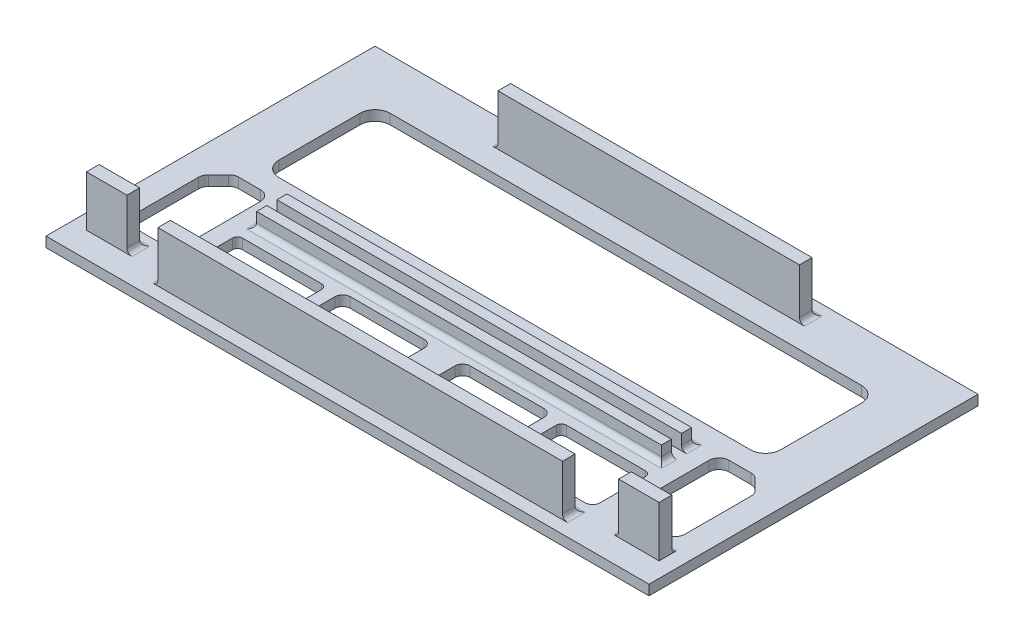
SolidWorks part; units mm, degrees
ref_plane "Front Plane" through (0, 0, 0) normal (0, 0, 1) x (1, 0, 0)
ref_plane "Top Plane" through (0, 0, 0) normal (0, 1, 0) x (1, 0, 0)
ref_plane "Right Plane" through (0, 0, 0) normal (1, 0, 0) x (0, 0, -1)
sketch "Sketch1" plane through (0, 0, 0) normal (0, 1, 0) x (1, 0, 0)
  line L1 (-59.6, -32.52) -> (59.6, -32.52)
  line L2 (-59.6, -32.52) -> (-59.6, 32.52)
  line L3 (-59.6, 32.52) -> (59.6, 32.52)
  line L4 (59.6, -32.52) -> (59.6, 32.52)
  line L5 (-59.6, -32.52) -> (59.6, 32.52) construction
  line L6 (-59.6, 32.52) -> (59.6, -32.52) construction
  point P0 (0, 0)
  dimension "D1" = 119.2
  dimension "D2" = 65.04
extrude "Boss-Extrude1" add sketch "Sketch1" along normal blind 2
ref_plane "Plane1" through (0, 0, 0) normal (-1, 0, 0) x (0, 0, 1)
sketch "Sketch2" plane through (0, 2, 0) normal (0, 1, 0) x (1, 0, 0)
  line L0 (-29.8, 29.52) -> (29.8, 29.52)
  line L1 (59.6, 32.52) -> (-59.6, 32.52) construction
  line L2 (59.6, -32.52) -> (59.6, 32.52) construction
  line L3 (59.6, -27.02) -> (59.6, -29.52)
  line L4 (29.8, 27.02) -> (-29.8, 27.02)
  line L5 (40, -4.48) -> (-40, -4.48)
  line L6 (40, -8.48) -> (40, -10.48)
  line L7 (-29.8, 29.52) -> (-29.8, 27.02)
  line L8 (29.8, 29.52) -> (29.8, 27.02)
  line L9 (-40, -4.48) -> (-40, -6.48)
  line L10 (-40, -6.48) -> (40, -6.48)
  line L11 (40, -6.48) -> (40, -4.48)
  line L12 (40, -10.48) -> (-40, -10.48)
  line L13 (-40, -10.48) -> (-40, -8.48)
  line L14 (-40, -8.48) -> (40, -8.48)
  line L15 (0, 1.1) -> (0, -1.1) construction
  point P16 (0, -10.48)
  dimension "D1" = 3
  dimension "D2" = 2.5
  dimension "D3" = 39
  dimension "D4" = 29.8
  dimension "D5" = 2
  dimension "D6" = 2
  dimension "D7" = 2
  dimension "D8" = 80
  dimension "D9" = 80
extrude "Boss-Extrude2" add sketch "Sketch2" along normal blind 10 contours L14 L13 L12 L6 | L10 L11 L5 L9 | L8 L0 L7 L4
fillet "Fillet1" radius 1 9 edges at (-29.8, 2, -28.27) (29.8, 2, -28.27) (0, 2, -29.52) (-40, 2, 5.48) (-40, 2, 9.48) (40, 2, 9.48) (40, 2, 5.48) (0, 2, 4.48) (0, 2, 10.48)
sketch "Sketch3" plane through (0, 12, 0) normal (0, 1, 0) x (1, 0, 0)
  line L0 (-40, -6.48) -> (40, -6.48) construction
  line L1 (40, -6.48) -> (40, -4.48) construction
  line L2 (40, -4.48) -> (-40, -4.48) construction
  line L3 (-40, -4.48) -> (-40, -6.48) construction
  line L4 (40, -8.48) -> (-40, -8.48) construction
  line L5 (-40, -8.48) -> (-40, -10.48) construction
  line L6 (-40, -10.48) -> (40, -10.48) construction
  line L7 (40, -10.48) -> (40, -8.48) construction
  line L8 (-40, -6.48) -> (40, -6.48)
  line L9 (40, -6.48) -> (40, -4.48)
  line L10 (40, -4.48) -> (-40, -4.48)
  line L11 (-40, -4.48) -> (-40, -6.48)
  line L12 (40, -8.48) -> (-40, -8.48)
  line L13 (-40, -8.48) -> (-40, -10.48)
  line L14 (-40, -10.48) -> (40, -10.48)
  line L15 (40, -10.48) -> (40, -8.48)
extrude "Cut-Extrude1" cut sketch "Sketch3" against normal blind 7
sketch "Sketch4" plane through (0, 2, 0) normal (0, 1, 0) x (1, 0, 0)
  line L0 (40, -30.02) -> (-40, -30.02)
  line L1 (-40, -30.02) -> (-40, -27.52)
  line L2 (-40, -27.52) -> (40, -27.52)
  line L3 (40, -27.52) -> (40, -30.02)
  line L4 (-59.6, -32.52) -> (59.6, -32.52) construction
  line L5 (0, 1.1) -> (0, -1.1) construction
  line L6 (48.6, -27.52) -> (56.6, -27.52)
  line L7 (56.6, -27.52) -> (56.6, -25.02)
  line L8 (56.6, -25.02) -> (48.6, -25.02)
  line L9 (48.6, -25.02) -> (48.6, -27.52)
  line L15 (59.6, -32.52) -> (59.6, 32.52) construction
  point P6 (0, -27.52)
  point P15 (52.6, -27.52)
  dimension "D1" = 2.5
  dimension "D2" = 2.5
  dimension "D3" = 80
  dimension "D4" = 2.5
  dimension "D6" = 3
  dimension "D7" = 8
extrude "Boss-Extrude3" add sketch "Sketch4" along normal blind 10
fillet "Fillet2" radius 1 5 edges at (-40, 2, 28.77) (48.6, 2, 26.27) (52.6, 2, 25.02) (40, 2, 28.77) (0, 2, 27.52)
mirror "Mirror1" about plane through (0, 0, 0) normal (-1, 0, 0) of "Boss-Extrude3"
fillet "Fillet3" radius 1 2 edges at (-52.6, 2, 25.02) (-48.6, 2, 26.27)
sketch "Sketch5" plane through (0, 2, 0) normal (0, 1, 0) x (1, 0, 0)
  line L0 (46.6, 22.52) -> (6.3115, 22.52)
  line L1 (6.3115, 22.52) -> (-46.6, 22.52)
  line L2 (-49.6, 19.52) -> (-49.6, 3.52)
  line L3 (-46.6, 0.52) -> (46.6, 0.52)
  line L4 (49.6, 3.52) -> (49.6, 19.52)
  line L5 (59.6, 32.52) -> (-59.6, 32.52) construction
  line L6 (59.6, -32.52) -> (59.6, 32.52) construction
  line L7 (-59.6, 32.52) -> (-59.6, -32.52) construction
  arc A0 (-49.6, 3.52) -> (-46.6, 0.52) centre (-46.6, 3.52) ccw
  arc A1 (-46.6, 22.52) -> (-49.6, 19.52) centre (-46.6, 19.52) ccw
  arc A2 (46.6, 22.52) -> (49.6, 19.52) centre (46.6, 19.52) cw
  arc A3 (46.6, 0.52) -> (49.6, 3.52) centre (46.6, 3.52) ccw
  dimension "D5" = 3
  dimension "D1" = 10
  dimension "D2" = 10
  dimension "D3" = 10
  dimension "D4" = 22
extrude "Cut-Extrude2" cut sketch "Sketch5" against normal blind 10
sketch "Sketch6" plane through (0, 2, 0) normal (0, 1, 0) x (1, 0, 0)
  line L3 (54.0142, -5.9408) -> (52.0453, -3.9719)
  line L4 (50.6311, -3.3862) -> (46.3278, -3.3862)
  line L5 (54.6, -7.3551) -> (54.6, -20.3979)
  line L6 (52.6, -22.3979) -> (46.3278, -22.3979)
  line L7 (44.3278, -20.3979) -> (44.3278, -5.3862)
  line L10 (39.8278, -13.4493) -> (24.2108, -13.4493)
  line L16 (4.044, -24.8936) -> (19.6609, -24.8936)
  line L17 (40.8278, -14.4493) -> (40.8278, -23.3936)
  line L18 (39.3278, -24.8936) -> (24.7108, -24.8936)
  line L19 (23.2108, -23.3936) -> (23.2108, -14.4493)
  line L21 (20.6609, -23.8936) -> (20.6609, -14.3214)
  line L22 (19.1609, -12.8214) -> (4.544, -12.8214)
  line L23 (3.044, -14.3214) -> (3.044, -23.8936)
  line L25 (59.6, -32.52) -> (59.6, 32.52) construction
  line L26 (0, -47.4967) -> (0, 52.968) construction
  line L29 (-4.044, -24.8936) -> (-19.6609, -24.8936)
  line L31 (-3.044, -14.3214) -> (-3.044, -23.8936)
  line L33 (-19.1609, -12.8214) -> (-4.544, -12.8214)
  line L34 (-20.6609, -23.8936) -> (-20.6609, -14.3214)
  line L37 (-39.3278, -24.8936) -> (-24.7108, -24.8936)
  line L39 (-39.8278, -13.4493) -> (-24.2108, -13.4493)
  line L40 (-23.2108, -14.4493) -> (-23.2108, -23.3936)
  line L42 (-40.8278, -23.3936) -> (-40.8278, -14.4493)
  line L43 (-44.3278, -5.3862) -> (-44.3278, -20.3979)
  line L44 (-50.6311, -3.3862) -> (-46.3278, -3.3862)
  line L45 (-54.0142, -5.9408) -> (-52.0453, -3.9719)
  line L46 (-54.6, -20.3979) -> (-54.6, -7.3551)
  line L51 (-52.6, -22.3979) -> (-46.3278, -22.3979)
  arc A1 (44.3278, -5.3862) -> (46.3278, -3.3862) centre (46.3278, -5.3862) cw
  arc A2 (52.0453, -3.9719) -> (50.6311, -3.3862) centre (50.6311, -5.3862) ccw
  arc A3 (54.6, -7.3551) -> (54.0142, -5.9408) centre (52.6, -7.3551) ccw
  arc A5 (46.3278, -22.3979) -> (44.3278, -20.3979) centre (46.3278, -20.3979) cw
  arc A8 (54.6, -20.3979) -> (52.6, -22.3979) centre (52.6, -20.3979) cw
  arc A10 (4.544, -12.8214) -> (3.044, -14.3214) centre (4.544, -14.3214) ccw
  arc A11 (20.6609, -14.3214) -> (19.1609, -12.8214) centre (19.1609, -14.3214) ccw
  arc A15 (24.7108, -24.8936) -> (23.2108, -23.3936) centre (24.7108, -23.3936) cw
  arc A16 (40.8278, -23.3936) -> (39.3278, -24.8936) centre (39.3278, -23.3936) cw
  arc A18 (3.044, -23.8936) -> (4.044, -24.8936) centre (4.044, -23.8936) ccw
  arc A19 (20.6609, -23.8936) -> (19.6609, -24.8936) centre (19.6609, -23.8936) cw
  arc A21 (40.8278, -14.4493) -> (39.8278, -13.4493) centre (39.8278, -14.4493) ccw
  arc A23 (24.2108, -13.4493) -> (23.2108, -14.4493) centre (24.2108, -14.4493) ccw
  arc A26 (-3.044, -23.8936) -> (-4.044, -24.8936) centre (-4.044, -23.8936) cw
  arc A27 (-20.6609, -23.8936) -> (-19.6609, -24.8936) centre (-19.6609, -23.8936) ccw
  arc A29 (-4.544, -12.8214) -> (-3.044, -14.3214) centre (-4.544, -14.3214) cw
  arc A31 (-20.6609, -14.3214) -> (-19.1609, -12.8214) centre (-19.1609, -14.3214) cw
  arc A35 (-40.8278, -23.3936) -> (-39.3278, -24.8936) centre (-39.3278, -23.3936) ccw
  arc A36 (-24.7108, -24.8936) -> (-23.2108, -23.3936) centre (-24.7108, -23.3936) ccw
  arc A37 (-24.2108, -13.4493) -> (-23.2108, -14.4493) centre (-24.2108, -14.4493) cw
  arc A40 (-40.8278, -14.4493) -> (-39.8278, -13.4493) centre (-39.8278, -14.4493) cw
  arc A41 (-44.3278, -5.3862) -> (-46.3278, -3.3862) centre (-46.3278, -5.3862) ccw
  arc A43 (-52.0453, -3.9719) -> (-50.6311, -3.3862) centre (-50.6311, -5.3862) cw
  arc A44 (-54.6, -7.3551) -> (-54.0142, -5.9408) centre (-52.6, -7.3551) cw
  arc A46 (-46.3278, -22.3979) -> (-44.3278, -20.3979) centre (-46.3278, -20.3979) ccw
  arc A49 (-54.6, -20.3979) -> (-52.6, -22.3979) centre (-52.6, -20.3979) ccw
  point P1 (-55.1167, -19.9138)
  point P2 (-43.7432, -20.3979)
  point P3 (-40.8278, -23.0111)
  point P9 (-23.2108, -23.0111)
  point P11 (0, 0)
  point P13 (0, 0)
  point P14 (-20.6609, -23.7181)
  point P16 (-2.8157, -23.8936)
  point P17 (0, 0)
  point P19 (23.5037, -13.7422)
  point P21 (0, 0)
  point P25 (45.1885, -5.3862)
  point P27 (0, 0)
  point P28 (54.0142, -5.3862)
  point P29 (0, 0)
  point P30 (40.5349, -13.7422)
  point P66 (3.044, -22.0111)
  point P71 (20.6609, -24.8936)
  point P74 (20.6609, -22.0111)
  dimension "D1" = 5
  dimension "D8" = 3.5
extrude "Cut-Extrude3" cut sketch "Sketch6" against normal blind 10
